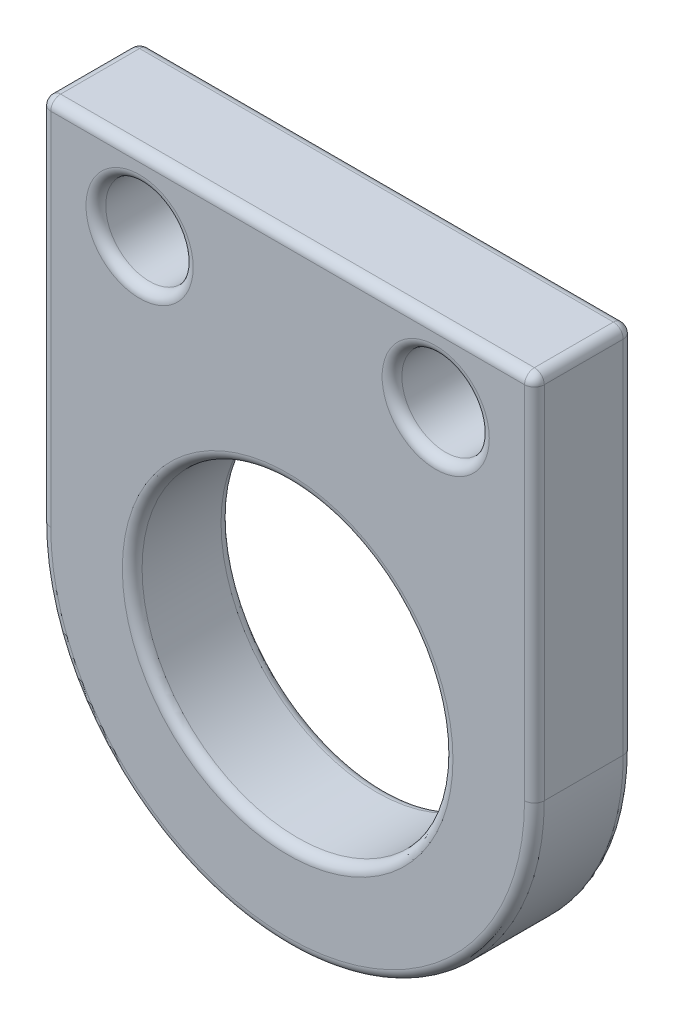
SolidWorks part; units mm, degrees
ref_plane "Front Plane" through (0, 0, 0) normal (0, 0, 1) x (1, 0, 0)
ref_plane "Top Plane" through (0, 0, 0) normal (0, 1, 0) x (1, 0, 0)
ref_plane "Right Plane" through (0, 0, 0) normal (1, 0, 0) x (0, 0, -1)
sketch "Sketch2" plane through (-2745.9112, -3464.7053, -5100.7827) normal (0, 0, 1) x (1, 0, 0)
  line L0 (-4.2552, -4.4563) -> (-4.2552, 5.0687) construction
  line L2 (-10.6052, -4.4563) -> (-10.6052, 5.0687)
  line L3 (-10.6052, 5.0687) -> (2.0948, 5.0687)
  line L4 (2.0948, -4.4563) -> (2.0948, 5.0687)
  line L5 (-10.6052, -4.4563) -> (2.0948, 5.0687) construction
  line L6 (-10.6052, 5.0687) -> (2.0948, -4.4563) construction
  arc A0 (-10.6052, -4.4563) -> (2.0948, -4.4563) centre (-4.2552, -4.4563) ccw
  point P0 (-4.2552, 0.3062)
  point P7 (2.0948, 5.0687)
  dimension "D2" = 6.35
  dimension "D1" = 9.525
  dimension "D3" = 2750.1664
  dimension "D4" = 3464.3991
extrude "Boss-Extrude1" add sketch "Sketch2" along normal blind 2.54
sketch "Sketch3" plane through (0, 0, -5098.2427) normal (0, 0, 1) x (1, 0, 0)
  line L0 (-2753.9764, -3461.5416) -> (-2746.3564, -3461.5416) construction
  line L1 (-2750.1664, -3469.1616) -> (-2750.1664, -3461.5416) construction
  circle A0 centre (-2750.1664, -3469.1616) radius 4
  circle A1 centre (-2746.3564, -3461.5416) radius 1.125
  circle A2 centre (-2753.9764, -3461.5416) radius 1.125
  point P7 (-2746.4029, -3461.5416)
  dimension "D1" = 8
  dimension "D3" = 2.25
  dimension "D4" = 2.25
  dimension "D2" = 7.62
  dimension "D5" = 7.62
extrude "Cut-Extrude1" cut sketch "Sketch3" against normal up to next
fillet "Fillet1" radius 0.254 16 edges at (-2743.8164, -3459.6366, -5099.5127) (-2756.5164, -3459.6366, -5099.5127) (-2750.1664, -3475.5116, -5098.2427) (-2756.5164, -3464.3991, -5098.2427) (-2750.1664, -3459.6366, -5098.2427) (-2743.8164, -3464.3991, -5098.2427) (-2752.8514, -3461.5416, -5098.2427) (-2745.2314, -3461.5416, -5098.2427) (-2746.1664, -3469.1616, -5098.2427) (-2750.1664, -3459.6366, -5100.7827) (-2756.5164, -3464.3991, -5100.7827) (-2750.1664, -3475.5116, -5100.7827) (-2743.8164, -3464.3991, -5100.7827) (-2752.8514, -3461.5416, -5100.7827) (-2745.2314, -3461.5416, -5100.7827) (-2746.1664, -3469.1616, -5100.7827)
equation "\"D3@Sketch3\"=2.25mm"
